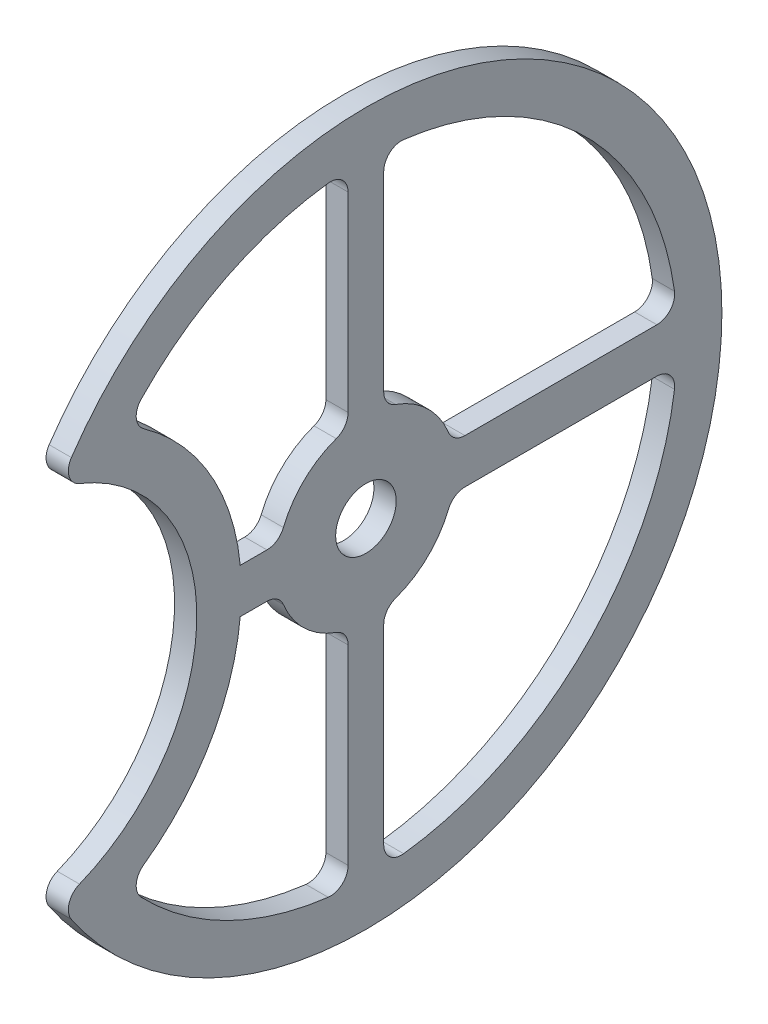
SolidWorks part; units mm, degrees
ref_plane "Front Plane" through (0, 0, 0) normal (0, 0, 1) x (1, 0, 0)
ref_plane "Top Plane" through (0, 0, 0) normal (0, 1, 0) x (1, 0, 0)
ref_plane "Right Plane" through (0, 0, 0) normal (1, 0, 0) x (0, 0, -1)
sketch "Sketch1" plane through (0, 0, 0) normal (1, 0, 0) x (0, 0, -1)
  line L1 (-2, 35) -> (-2, -35)
  line L2 (0, -2.5) -> (-14.1205, -2.5)
  line L3 (0, -2.5) -> (34.9106, -2.5)
  line L4 (0, 2.5) -> (-14.1205, 2.5)
  line L5 (0, 2.5) -> (34.9106, 2.5)
  line L6 (39.9218, 2.5) -> (40, 2.5)
  line L7 (39.9218, -2.5) -> (40, -2.5)
  line L8 (2, 35) -> (2, -35)
  arc A0 (-34.4875, -20.2636) -> (-34.4875, 20.2636) centre (0, 0) ccw
  circle A1 centre (0, 0) radius 1.6
  arc A2 (-34.4875, -20.2636) -> (-34.4875, 20.2636) centre (-40, 0) ccw
  arc A3 (-26.8625, -22.4367) -> (-26.8625, 22.4367) centre (-40, 0) ccw
  arc A4 (-26.8625, -22.4367) -> (-2, -34.9428) centre (0, 0) ccw
  circle A5 centre (0, 0) radius 10
  arc A6 (-2, 34.9428) -> (-26.8625, 22.4367) centre (0, 0) ccw
  circle A7 centre (-40, 0) radius 26 construction
  circle A8 centre (-40, 0) radius 21 construction
  circle A9 centre (0, 0) radius 40 construction
  circle A10 centre (0, 0) radius 35 construction
  arc A11 (2, -34.9428) -> (2, 34.9428) centre (0, 0) ccw
  point P1 (35, 0)
  point P5 (38.2522, 11.6949)
  point P7 (-19.9176, 6.1398)
  point P11 (-15.1361, 7.6017)
  point P14 (40, 0)
  point P20 (-40, -2.5)
  point P24 (-40, 2.5)
  dimension "D1" = 80
  dimension "D2" = 3.2
  dimension "D3" = 42
  dimension "D6" = 20
  dimension "D4" = 5
  dimension "D5" = 5
extrude "Boss-Extrude1" add sketch "Sketch1" along normal blind 2.5
fillet "Fillet1" radius 2 18 edges at (1.25, 2.5, 9.6825) (1.25, -2.5, 9.6825) (1.25, 9.798, 2) (1.25, -9.798, 2) (1.25, 34.9428, -2) (1.25, -34.9428, -2) (1.25, -34.9428, 2) (1.25, -22.4367, 26.8625) (1.25, 22.4367, 26.8625) (1.25, 9.798, -2) (1.25, -9.798, -2) (1.25, 2.5, -9.6825) (1.25, -2.5, -9.6825) (1.25, -2.5, -34.9106) (1.25, 2.5, -34.9106) (1.25, 34.9428, 2) (1.25, -20.2636, 34.4875) (1.25, 20.2636, 34.4875)
sketch "Sketch2" plane through (0, 0, 0) normal (-1, 0, 0) x (0, 0, 1)
  circle A0 centre (0, 0) radius 3.4
  dimension "D1" = 6.8
extrude "Cut-Extrude1" cut sketch "Sketch2" against normal through all
